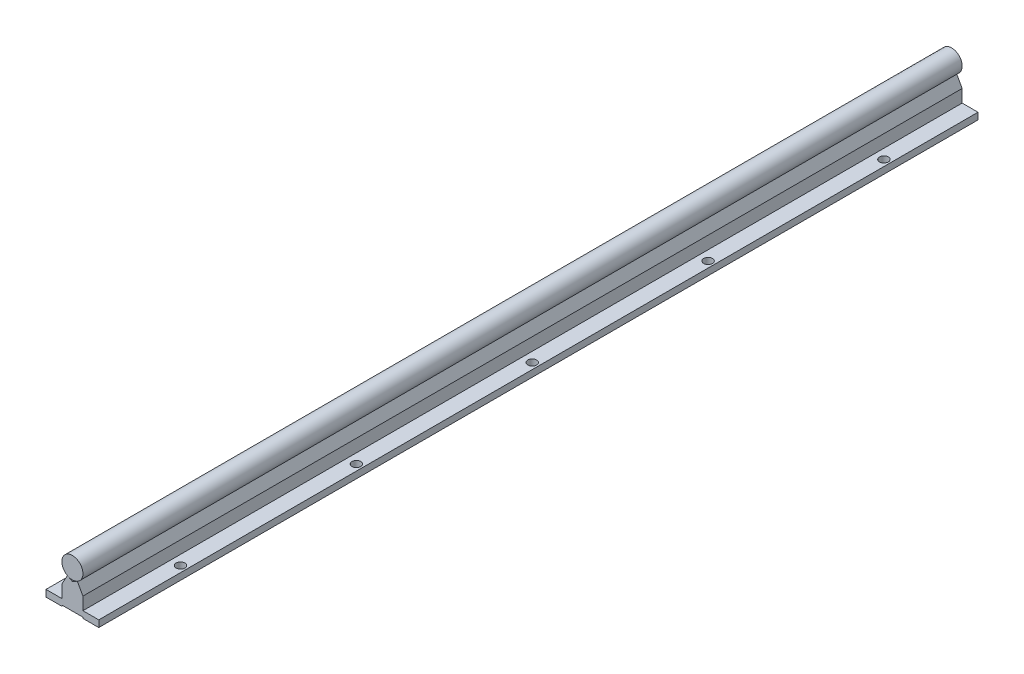
SolidWorks part; units mm, degrees
ref_plane "Alzado" through (0, 0, 0) normal (0, 0, 1) x (1, 0, 0)
ref_plane "Planta" through (0, 0, 0) normal (0, 1, 0) x (1, 0, 0)
ref_plane "Vista lateral" through (0, 0, 0) normal (1, 0, 0) x (0, 0, -1)
sketch "Croquis1" plane through (0, 0, 0) normal (0, 0, 1) x (1, 0, 0)
  line L0 (0, 0) -> (0, -22) construction
  line L1 (0, -22) -> (15, -22) construction
  line L2 (3.5, 0) -> (3.5, -22) construction
  line L3 (6, -22) -> (6, 5.4102) construction
  line L4 (-13.9204, -11) -> (10.0172, -11) construction
  line L5 (0, -6.8) -> (2.8235, -5.2941)
  line L6 (2.8235, -5.2941) -> (6, -11)
  line L7 (6, -11) -> (6, -18.2)
  line L8 (6, -18.2) -> (15, -18.2)
  line L9 (15, -18.2) -> (15, -22)
  line L10 (-6, -21.4) -> (6, -21.4)
  line L11 (6, -21.4) -> (6, -22)
  line L12 (6, -22) -> (15, -22)
  line L13 (-6, -21.4) -> (-6, -22)
  line L14 (-6, -22) -> (-15, -22)
  line L15 (-15, -18.2) -> (-15, -22)
  line L16 (-6, -18.2) -> (-15, -18.2)
  line L17 (-6, -11) -> (-6, -18.2)
  line L18 (-2.8235, -5.2941) -> (-6, -11)
  line L19 (0, -6.8) -> (-2.8235, -5.2941)
  circle A0 centre (0, 0) radius 6
  point P17 (0, -6)
  point P21 (0, -21.4)
  dimension "D1" = 12
  dimension "D2" = 22
  dimension "D3" = 15
  dimension "D4" = 3.5
  dimension "D5" = 6
  dimension "D6" = 11
  dimension "D7" = 0.8
  dimension "D8" = 3.8
  dimension "D9" = 0.6
extrude "Saliente-Extruir1" add sketch "Croquis1" along normal blind 500 contours L5 L19 L18 L17 L16 L15 L14 L13 L10 L11 L12 L9 L8 L7 L6 | A0
sketch "Croquis2" plane through (0, -18.2, 0) normal (0, 1, 0) x (1, 0, 0)
  line L0 (-11.5, 0) -> (-11.5, -500) construction
  line L1 (-6, 0) -> (-15, 0) construction
  line L2 (-6, -500) -> (-15, -500) construction
  line L3 (-15, -500) -> (-15, 0) construction
  circle A0 centre (-11.5, -50) radius 2.5
  circle A1 centre (-11.5, -150) radius 2.5
  circle A2 centre (-11.5, -250) radius 2.5
  circle A3 centre (-11.5, -350) radius 2.5
  circle A4 centre (-11.5, -450) radius 2.5
  dimension "D2" = 5
  dimension "D1" = 3.5
  dimension "D3" = 50
  dimension "D4" = 5
extrude "Cortar-Extruir1" cut sketch "Croquis2" against normal up to surface (3.8 mm away) up to face at (-10.5, -22, 250)
mirror "Simetría1" about plane through (0, 0, 0) normal (1, 0, 0) of "Cortar-Extruir1"
ref_plane "Plano1" through (0, 0, 250) normal (0, 0, -1) x (-1, 0, 0)
equation "\"D4@Croquis1\"=7/2"
